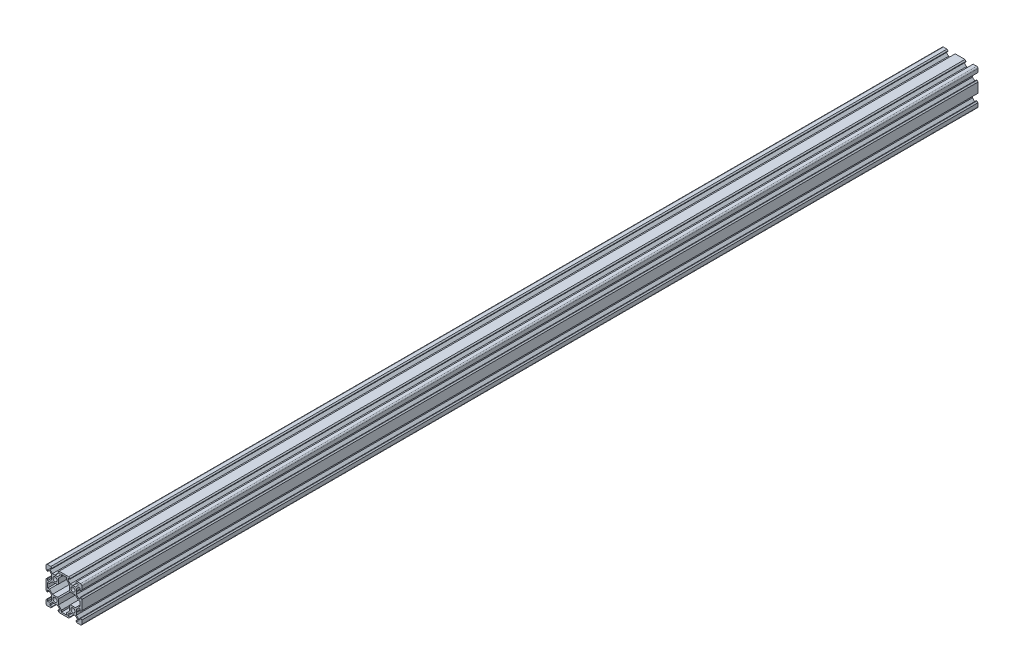
SolidWorks part; units mm, degrees
material "6061-T6 (SS)"
ref_plane "Front Plane" through (0, 0, 0) normal (0, 0, 1) x (1, 0, 0)
ref_plane "Top Plane" through (0, 0, 0) normal (0, 1, 0) x (1, 0, 0)
ref_plane "Right Plane" through (0, 0, 0) normal (1, 0, 0) x (0, 0, -1)
sketch "Sketch1" plane through (0, 0, 0) normal (0, 0, 1) x (1, 0, 0)
  line L1 (18.5, -20) -> (-18.5, -20)
  line L2 (20, -18.5) -> (20, 18.5)
  line L3 (18.5, 20) -> (-18.5, 20)
  line L4 (-20, -18.5) -> (-20, 18.5)
  line L5 (20, -20) -> (-20, 20) construction
  line L6 (20, 20) -> (-20, -20) construction
  circle A0 centre (-10, 10) radius 2.3
  circle A1 centre (10, -10) radius 2.3
  circle A2 centre (10, 10) radius 2.3
  circle A3 centre (-10, -10) radius 2.3
  arc A4 (-18.5, -20) -> (-20, -18.5) centre (-18.5, -18.5) cw
  arc A5 (18.5, -20) -> (20, -18.5) centre (18.5, -18.5) ccw
  arc A6 (20, 18.5) -> (18.5, 20) centre (18.5, 18.5) ccw
  arc A7 (-18.5, 20) -> (-20, 18.5) centre (-18.5, 18.5) ccw
  point P0 (0, 0)
  line B0 (-10, 10) -> (-10, 20) construction
  line B1 (-10, 13.69) -> (-10.21, 13.9)
  line B2 (-10.21, 13.9) -> (-12.8393, 13.9)
  line B3 (-12.8393, 13.9) -> (-15.5, 16.5607)
  line B4 (-15.5, 16.5607) -> (-15.5, 18.2)
  line B5 (-15.5, 18.2) -> (-13.395, 18.2)
  line B6 (-13.395, 18.2) -> (-13.395, 18.815)
  line B7 (-13.395, 18.815) -> (-14.58, 20)
  line B8 (-14.58, 20) -> (-5.42, 20)
  line B9 (-10, 10) -> (-15.9132, 15.9132) construction
  line B10 (-6.605, 18.815) -> (-5.42, 20)
  line B11 (-6.605, 18.2) -> (-6.605, 18.815)
  line B12 (-4.5, 18.2) -> (-6.605, 18.2)
  line B13 (-4.5, 16.5607) -> (-4.5, 18.2)
  line B14 (-7.1607, 13.9) -> (-4.5, 16.5607)
  line B15 (-9.79, 13.9) -> (-7.1607, 13.9)
  line B16 (-10, 13.69) -> (-9.79, 13.9)
  line B17 (10, 10) -> (10, 20) construction
  line B18 (10, 13.69) -> (9.79, 13.9)
  line B19 (9.79, 13.9) -> (7.1607, 13.9)
  line B20 (7.1607, 13.9) -> (4.5, 16.5607)
  line B21 (4.5, 16.5607) -> (4.5, 18.2)
  line B22 (4.5, 18.2) -> (6.605, 18.2)
  line B23 (6.605, 18.2) -> (6.605, 18.815)
  line B24 (6.605, 18.815) -> (5.42, 20)
  line B25 (5.42, 20) -> (14.58, 20)
  line B26 (10, 10) -> (4.0868, 15.9132) construction
  line B27 (13.395, 18.815) -> (14.58, 20)
  line B28 (13.395, 18.2) -> (13.395, 18.815)
  line B29 (15.5, 18.2) -> (13.395, 18.2)
  line B30 (15.5, 16.5607) -> (15.5, 18.2)
  line B31 (12.8393, 13.9) -> (15.5, 16.5607)
  line B32 (10.21, 13.9) -> (12.8393, 13.9)
  line B33 (10, 13.69) -> (10.21, 13.9)
  line B34 (-10, 10) -> (-20, 10) construction
  line B35 (-13.69, 10) -> (-13.9, 9.79)
  line B36 (-13.9, 9.79) -> (-13.9, 7.1607)
  line B37 (-13.9, 7.1607) -> (-16.5607, 4.5)
  line B38 (-16.5607, 4.5) -> (-18.2, 4.5)
  line B39 (-18.2, 4.5) -> (-18.2, 6.605)
  line B40 (-18.2, 6.605) -> (-18.815, 6.605)
  line B41 (-18.815, 6.605) -> (-20, 5.42)
  line B42 (-20, 5.42) -> (-20, 14.58)
  line B43 (-10, 10) -> (-15.9132, 4.0868) construction
  line B44 (-18.815, 13.395) -> (-20, 14.58)
  line B45 (-18.2, 13.395) -> (-18.815, 13.395)
  line B46 (-18.2, 15.5) -> (-18.2, 13.395)
  line B47 (-16.5607, 15.5) -> (-18.2, 15.5)
  line B48 (-13.9, 12.8393) -> (-16.5607, 15.5)
  line B49 (-13.9, 10.21) -> (-13.9, 12.8393)
  line B50 (-13.69, 10) -> (-13.9, 10.21)
  line B51 (-10, -10) -> (-20, -10) construction
  line B52 (-13.69, -10) -> (-13.9, -10.21)
  line B53 (-13.9, -10.21) -> (-13.9, -12.8393)
  line B54 (-13.9, -12.8393) -> (-16.5607, -15.5)
  line B55 (-16.5607, -15.5) -> (-18.2, -15.5)
  line B56 (-18.2, -15.5) -> (-18.2, -13.395)
  line B57 (-18.2, -13.395) -> (-18.815, -13.395)
  line B58 (-18.815, -13.395) -> (-20, -14.58)
  line B59 (-20, -14.58) -> (-20, -5.42)
  line B60 (-10, -10) -> (-15.9132, -15.9132) construction
  line B61 (-18.815, -6.605) -> (-20, -5.42)
  line B62 (-18.2, -6.605) -> (-18.815, -6.605)
  line B63 (-18.2, -4.5) -> (-18.2, -6.605)
  line B64 (-16.5607, -4.5) -> (-18.2, -4.5)
  line B65 (-13.9, -7.1607) -> (-16.5607, -4.5)
  line B66 (-13.9, -9.79) -> (-13.9, -7.1607)
  line B67 (-13.69, -10) -> (-13.9, -9.79)
  line B68 (-10, -10) -> (-10, -20) construction
  line B69 (-10, -13.69) -> (-9.79, -13.9)
  line B70 (-9.79, -13.9) -> (-7.1607, -13.9)
  line B71 (-7.1607, -13.9) -> (-4.5, -16.5607)
  line B72 (-4.5, -16.5607) -> (-4.5, -18.2)
  line B73 (-4.5, -18.2) -> (-6.605, -18.2)
  line B74 (-6.605, -18.2) -> (-6.605, -18.815)
  line B75 (-6.605, -18.815) -> (-5.42, -20)
  line B76 (-5.42, -20) -> (-14.58, -20)
  line B77 (-10, -10) -> (-4.0868, -15.9132) construction
  line B78 (-13.395, -18.815) -> (-14.58, -20)
  line B79 (-13.395, -18.2) -> (-13.395, -18.815)
  line B80 (-15.5, -18.2) -> (-13.395, -18.2)
  line B81 (-15.5, -16.5607) -> (-15.5, -18.2)
  line B82 (-12.8393, -13.9) -> (-15.5, -16.5607)
  line B83 (-10.21, -13.9) -> (-12.8393, -13.9)
  line B84 (-10, -13.69) -> (-10.21, -13.9)
  line B85 (10, -10) -> (10, -20) construction
  line B86 (10, -13.69) -> (10.21, -13.9)
  line B87 (10.21, -13.9) -> (12.8393, -13.9)
  line B88 (12.8393, -13.9) -> (15.5, -16.5607)
  line B89 (15.5, -16.5607) -> (15.5, -18.2)
  line B90 (15.5, -18.2) -> (13.395, -18.2)
  line B91 (13.395, -18.2) -> (13.395, -18.815)
  line B92 (13.395, -18.815) -> (14.58, -20)
  line B93 (14.58, -20) -> (5.42, -20)
  line B94 (10, -10) -> (15.9132, -15.9132) construction
  line B95 (6.605, -18.815) -> (5.42, -20)
  line B96 (6.605, -18.2) -> (6.605, -18.815)
  line B97 (4.5, -18.2) -> (6.605, -18.2)
  line B98 (4.5, -16.5607) -> (4.5, -18.2)
  line B99 (7.1607, -13.9) -> (4.5, -16.5607)
  line B100 (9.79, -13.9) -> (7.1607, -13.9)
  line B101 (10, -13.69) -> (9.79, -13.9)
  line B102 (10, 10) -> (20, 10) construction
  line B103 (13.69, 10) -> (13.9, 10.21)
  line B104 (13.9, 10.21) -> (13.9, 12.8393)
  line B105 (13.9, 12.8393) -> (16.5607, 15.5)
  line B106 (16.5607, 15.5) -> (18.2, 15.5)
  line B107 (18.2, 15.5) -> (18.2, 13.395)
  line B108 (18.2, 13.395) -> (18.815, 13.395)
  line B109 (18.815, 13.395) -> (20, 14.58)
  line B110 (20, 14.58) -> (20, 5.42)
  line B111 (10, 10) -> (15.9132, 15.9132) construction
  line B112 (18.815, 6.605) -> (20, 5.42)
  line B113 (18.2, 6.605) -> (18.815, 6.605)
  line B114 (18.2, 4.5) -> (18.2, 6.605)
  line B115 (16.5607, 4.5) -> (18.2, 4.5)
  line B116 (13.9, 7.1607) -> (16.5607, 4.5)
  line B117 (13.9, 9.79) -> (13.9, 7.1607)
  line B118 (13.69, 10) -> (13.9, 9.79)
  line B119 (10, -10) -> (20, -10) construction
  line B120 (13.69, -10) -> (13.9, -9.79)
  line B121 (13.9, -9.79) -> (13.9, -7.1607)
  line B122 (13.9, -7.1607) -> (16.5607, -4.5)
  line B123 (16.5607, -4.5) -> (18.2, -4.5)
  line B124 (18.2, -4.5) -> (18.2, -6.605)
  line B125 (18.2, -6.605) -> (18.815, -6.605)
  line B126 (18.815, -6.605) -> (20, -5.42)
  line B127 (20, -5.42) -> (20, -14.58)
  line B128 (10, -10) -> (15.9132, -4.0868) construction
  line B129 (18.815, -13.395) -> (20, -14.58)
  line B130 (18.2, -13.395) -> (18.815, -13.395)
  line B131 (18.2, -15.5) -> (18.2, -13.395)
  line B132 (16.5607, -15.5) -> (18.2, -15.5)
  line B133 (13.9, -12.8393) -> (16.5607, -15.5)
  line B134 (13.9, -10.21) -> (13.9, -12.8393)
  line B135 (13.69, -10) -> (13.9, -10.21)
  line B136 (-18.2, -2.7) -> (-18.2, 2.7)
  line B137 (-18.2, 2.7) -> (-16.2393, 2.7)
  line B138 (-16.2393, 2.7) -> (-12.8393, 6.1)
  line B139 (-12.8393, 6.1) -> (-7.1607, 6.1)
  line B140 (-10, 6.1) -> (-10, 0) construction
  line B141 (-10, 0) -> (-18.2, 0) construction
  line B142 (-12.8393, -6.1) -> (-7.1607, -6.1)
  line B143 (-16.2393, -2.7) -> (-12.8393, -6.1)
  line B144 (-18.2, -2.7) -> (-16.2393, -2.7)
  line B145 (-10, 6.1) -> (-10, 10) construction
  line B146 (-10, 10) -> (-15.0927, 4.9073) construction
  line B147 (-10, 10) -> (-6.3747, 6.3747) construction
  line B148 (2.7, 18.2) -> (2.7, 16.2393)
  line B149 (2.7, 16.2393) -> (6.1, 12.8393)
  line B150 (6.1, 12.8393) -> (6.1, 7.1607)
  line B151 (-6.1, 12.8393) -> (-6.1, 7.1607)
  line B152 (-2.7, 16.2393) -> (-6.1, 12.8393)
  line B153 (-2.7, 18.2) -> (-2.7, 16.2393)
  line B154 (2.7, 18.2) -> (-2.7, 18.2)
  line B155 (2.7, -18.2) -> (-2.7, -18.2)
  line B156 (-2.7, -18.2) -> (-2.7, -16.2393)
  line B157 (-2.7, -16.2393) -> (-6.1, -12.8393)
  line B158 (-6.1, -12.8393) -> (-6.1, -7.1607)
  line B159 (6.1, -12.8393) -> (6.1, -7.1607)
  line B160 (2.7, -16.2393) -> (6.1, -12.8393)
  line B161 (2.7, -18.2) -> (2.7, -16.2393)
  line B162 (0, 18.2) -> (0, -18.2) construction
  line B163 (12.8393, -6.1) -> (7.1607, -6.1)
  line B164 (16.2393, -2.7) -> (12.8393, -6.1)
  line B165 (18.2, -2.7) -> (16.2393, -2.7)
  line B166 (18.2, -2.7) -> (18.2, 2.7)
  line B167 (18.2, 2.7) -> (16.2393, 2.7)
  line B168 (16.2393, 2.7) -> (12.8393, 6.1)
  line B169 (12.8393, 6.1) -> (7.1607, 6.1)
  line B170 (-7.1607, 6.1) -> (-6.1, 7.1607)
  line B171 (6.1, 7.1607) -> (7.1607, 6.1)
  line B172 (7.1607, -6.1) -> (6.1, -7.1607)
  line B173 (-6.1, -7.1607) -> (-7.1607, -6.1)
  dimension "D4" = 4.6
  dimension "D5" = 1.5
  dimension "D1" = 40
  dimension "D2" = 10
  dimension "D3" = 10
sketch_block_instance "V Slot 2-1"
sketch_block "V Slot 2" parameters "D1"=10, "D2"=11, "D3"=4.3, "D4"=1.8, "D5"=0.21, "D6"=45, "D7"=9.16, "D8"=1.5, "D9"=6.79
sketch_block_instance "V Slot 2-2"
sketch_block_instance "V Slot 2-3"
sketch_block_instance "V Slot 2-4"
sketch_block_instance "V Slot 2-5"
sketch_block_instance "V Slot 2-6"
sketch_block_instance "V Slot 2-7"
sketch_block_instance "V Slot 2-8"
sketch_block_instance "Center Cutout 2-1"
sketch_block "Center Cutout 2" parameters "D1"=5.4, "D2"=12.2, "D3"=8.2, "D4"=45, "D5"=10, "D6"=1.5
extrude "Boss-Extrude1" add sketch "Sketch1" along normal blind 1000 contours B135 B120 B121 B122 B123 B124 B125 B126 L2 B112 B113 B114 B115 B116 B117 B118 B103 B104 B105 B106 B107 B108 B109 A6 L3 B27 B28 B29 B30 B31 B32 B33 B18 B19 B20 B21 B22 B23 B24 B10 B11 B12 B13 B14 B15 B16 B1 B2 B3
